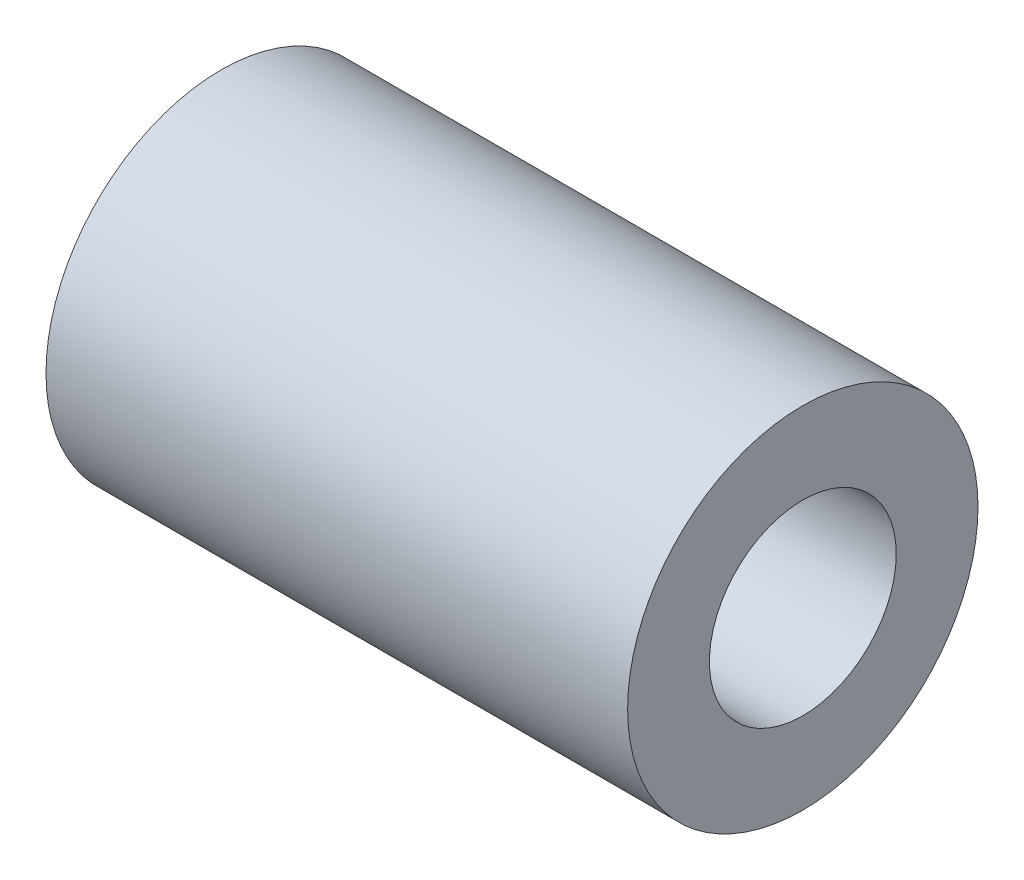
SolidWorks part; units mm, degrees
ref_plane "Alzado" through (0, 0, 0) normal (0, 0, 1) x (1, 0, 0)
ref_plane "Planta" through (0, 0, 0) normal (0, 1, 0) x (1, 0, 0)
ref_plane "Vista lateral" through (0, 0, 0) normal (1, 0, 0) x (0, 0, -1)
sketch "Croquis1" plane through (0, 0, 0) normal (1, 0, 0) x (0, 0, -1)
  circle A0 centre (0, 0) radius 4
  circle A1 centre (0, 0) radius 7.5
  dimension "D1" = 8
  dimension "D2" = 15
extrude "Saliente-Extruir1" add sketch "Croquis1" along normal blind 24.9
